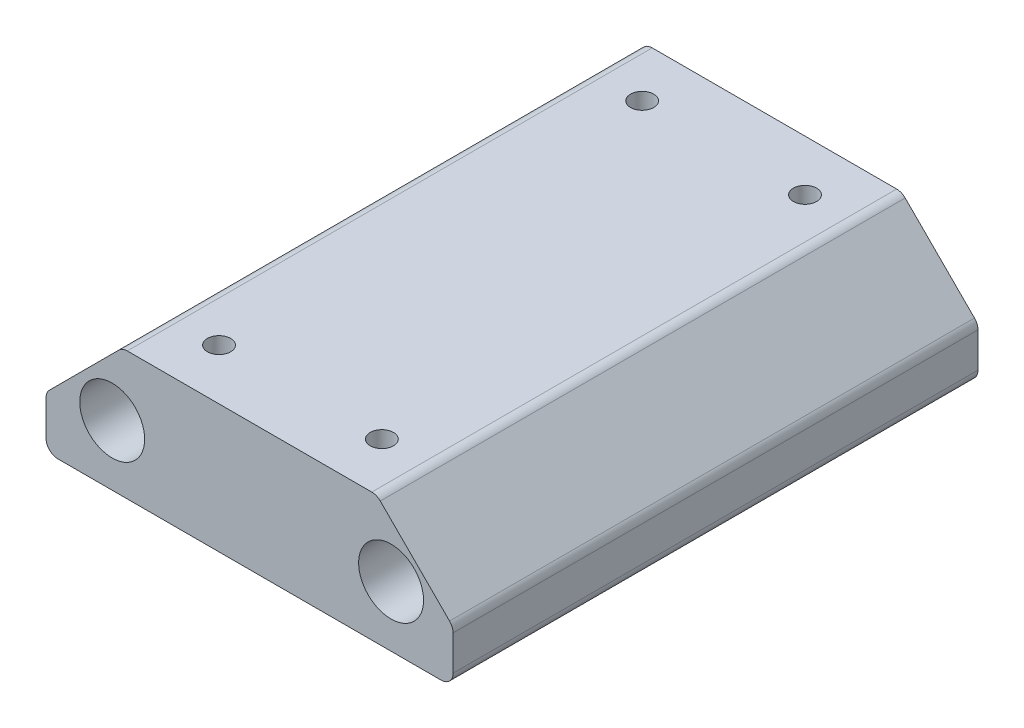
SolidWorks part; units mm, degrees
ref_plane "Front Plane" through (0, 0, 0) normal (0, 0, 1) x (1, 0, 0)
ref_plane "Top Plane" through (0, 0, 0) normal (0, 1, 0) x (1, 0, 0)
ref_plane "Right Plane" through (0, 0, 0) normal (1, 0, 0) x (0, 0, -1)
sketch "Sketch1" plane through (0, 0, 0) normal (0, 0, 1) x (1, 0, 0)
  line L1 (-25.6621, -156.15) -> (25.1379, -156.15)
  line L2 (-25.6621, -156.15) -> (-25.6621, -140.15)
  line L3 (-25.6621, -140.15) -> (25.1379, -140.15)
  line L4 (25.1379, -156.15) -> (25.1379, -140.15)
  circle A2 centre (-17.4, -148.6184) radius 4.05
  circle A3 centre (17.4, -148.6184) radius 4.05
  dimension "D1" = 16
  dimension "D2" = 50.8
extrude "Boss-Extrude1" add sketch "Sketch1" along normal up to surface (65.5 mm away)
fillet "Fillet1" radius 1.5 2 edges at (-25.6621, -156.15, 32.75) (25.1379, -156.15, 32.75)
chamfer "Chamfer1" distance 9.525 angle 45 2 edges at (25.1379, -140.15, 32.75) (-25.6621, -140.15, 32.75)
fillet "Fillet2" radius 1.5 4 edges at (25.1379, -149.675, 32.75) (15.6129, -140.15, 32.75) (-16.1371, -140.15, 32.75) (-25.6621, -149.675, 32.75)
sketch "Sketch3" plane through (0, -156.15, 0) normal (0, -1, 0) x (1, 0, 0)
  line L0 (-24.1621, 65.5) -> (23.6379, 65.5) construction
  line L1 (-10.4221, 59.15) -> (9.8979, 59.15) construction
  line L2 (-10.4221, 59.15) -> (-10.4221, 6.35) construction
  line L3 (-10.4221, 6.35) -> (9.8979, 6.35) construction
  line L4 (9.8979, 59.15) -> (9.8979, 6.35) construction
  line L5 (-24.1621, 0) -> (23.6379, 0) construction
  line L6 (25.1379, 65.5) -> (25.1379, 0) construction
  line L7 (-25.6621, 0) -> (-25.6621, 65.5) construction
  circle A0 centre (-10.4221, 59.15) radius 1.45
  circle A1 centre (9.8979, 59.15) radius 1.45
  circle A2 centre (-10.4221, 6.35) radius 1.45
  circle A3 centre (9.8979, 6.35) radius 1.45
  dimension "D1" = 2.9
  dimension "D2" = 6.35
  dimension "D3" = 6.35
  dimension "D4" = 15.24
  dimension "D5" = 15.24
extrude "Cut-Extrude1" cut sketch "Sketch3" against normal through all
ref_plane "Plane1" through (-45.4237, -144.0655, 0) normal (-0.3007, -0.9537, 0) x (0, 0, -1)
sketch "Sketch4" plane through (-45.4237, -144.0655, 0) normal (-0.3007, -0.9537, 0) x (0, 0, -1)
  line L0 (0, 20.7206) -> (-38.1, 20.7206)
  line L1 (0, 20.7206) -> (0, -26.9044)
  line L2 (-38.1, 20.7206) -> (-38.1, -26.9044)
  line L3 (0, -26.9044) -> (-38.1, -26.9044)
  line L4 (-65.5, 20.7206) -> (0, 20.7206) construction
  dimension "D1" = 38.1
  dimension "D2" = 47.625
extrude "Boss-Extrude2" [suppressed] add sketch "Sketch4" against normal blind 6
sketch "Sketch5" [suppressed] plane through (0, 0, 0) normal (0, 0, -1) x (-1, 0, 0)
  line L0 (25.2227, -149.2356) -> (16.5764, -140.5893) construction
  line L1 (23.8579, -144.574) -> (25.3908, -149.4359) construction
  line L2 (25.2227, -149.2356) -> (21.3514, -145.3643)
  line L3 (23.8579, -144.574) -> (25.3908, -149.4359)
  line L4 (23.8579, -144.574) -> (21.3514, -145.3643)
  line L5 (69.2786, -130.2529) -> (23.8579, -144.574) construction
  arc A0 (25.3908, -149.4359) -> (25.2227, -149.2356) centre (24.1621, -150.2963) ccw construction
  arc A1 (25.3908, -149.4359) -> (25.2227, -149.2356) centre (24.1621, -150.2963) ccw
extrude "Boss-Extrude3" [suppressed] add sketch "Sketch5" against normal up to surface (38.1 mm away)
fillet "Fillet3" [suppressed] radius 2.54
fillet "Fillet5" [suppressed] radius 50.8
fillet "Fillet6" [suppressed] radius 12.7
sketch "Sketch7" [suppressed] plane through (-45.4237, -144.0655, 0) normal (-0.3007, -0.9537, 0) x (0.9537, -0.3007, 0)
  line L0 (-18.9044, 0) -> (4.0956, 0)
  line L1 (-18.9044, 0) -> (-18.9044, 28)
  line L2 (4.0956, 0) -> (4.0956, 28)
  line L3 (-17.4044, 29.5) -> (2.5956, 29.5)
  line L4 (-26.9044, 0) -> (20.7206, 0) construction
  line L5 (-26.9044, 38.1) -> (-26.9044, 0) construction
  arc A0 (4.0956, 28) -> (2.5956, 29.5) centre (2.5956, 28) ccw
  arc A1 (-18.9044, 28) -> (-17.4044, 29.5) centre (-17.4044, 28) cw
  point P10 (4.0956, 29.5)
  point P13 (-18.9044, 29.5)
  dimension "D4" = 1.5
  dimension "D1" = 8
  dimension "D2" = 23
  dimension "D3" = 29.5
extrude "Cut-Extrude3" [suppressed] cut sketch "Sketch7" against normal blind 6
sketch "Sketch9" [suppressed] plane through (-45.4237, -144.0655, 0) normal (-0.3007, -0.9537, 0) x (0.9537, -0.3007, 0)
  line L0 (-3.0919, 0) -> (-3.0919, 4.625) construction
  line L1 (-26.9044, 0) -> (20.7206, 0) construction
  line L2 (-7.7169, 0) -> (-7.7169, 4.625)
  line L3 (1.5331, 0) -> (1.5331, 4.625)
  arc A0 (-7.7169, 0) -> (1.5331, 0) centre (-3.0919, 0) ccw
  arc A1 (1.5331, 4.625) -> (-7.7169, 4.625) centre (-3.0919, 4.625) ccw
  point P4 (-3.0919, 2.3125)
  dimension "D1" = 4.625
  dimension "D2" = 4.625
extrude "Cut-Extrude4" [suppressed] cut sketch "Sketch9" against normal through all
sketch "Sketch10" plane through (0, 0, 0) normal (0, 0, -1) x (-1, 0, 0)
  line L8 (25.6621, -154.65) -> (25.6621, -150.2963)
  line L16 (25.6621, -154.65) -> (25.6621, -150.2963)
  line L19 (25.2227, -149.2356) -> (16.5764, -140.5893)
  line L20 (25.2227, -149.2356) -> (16.5764, -140.5893)
  line L21 (15.5158, -140.15) -> (-14.9916, -140.15)
  line L22 (15.5158, -140.15) -> (-14.9916, -140.15)
  line L23 (-16.0523, -140.5893) -> (-24.6986, -149.2356)
  line L24 (-16.0523, -140.5893) -> (-24.6986, -149.2356)
  line L25 (-25.1379, -150.2963) -> (-25.1379, -154.65)
  line L26 (-25.1379, -150.2963) -> (-25.1379, -154.65)
  line L27 (-23.6379, -156.15) -> (24.1621, -156.15)
  line L28 (-23.6379, -156.15) -> (24.1621, -156.15)
  arc A1 (26.6378, -150.0539) -> (143.2694, 51.9579) centre (0, 0) ccw construction
  arc A2 (64.6781, -137.9946) -> (70.767, -134.9733) centre (0, 0) ccw
  arc A8 (25.6621, -150.2963) -> (25.2227, -149.2356) centre (24.1621, -150.2963) ccw
  arc A9 (25.6621, -150.2963) -> (25.2227, -149.2356) centre (24.1621, -150.2963) ccw
  arc A10 (16.5764, -140.5893) -> (15.5158, -140.15) centre (15.5158, -141.65) ccw
  arc A11 (16.5764, -140.5893) -> (15.5158, -140.15) centre (15.5158, -141.65) ccw
  arc A12 (-14.9916, -140.15) -> (-16.0523, -140.5893) centre (-14.9916, -141.65) ccw
  arc A13 (-14.9916, -140.15) -> (-16.0523, -140.5893) centre (-14.9916, -141.65) ccw
  arc A14 (-24.6986, -149.2356) -> (-25.1379, -150.2963) centre (-23.6379, -150.2963) ccw
  arc A15 (-24.6986, -149.2356) -> (-25.1379, -150.2963) centre (-23.6379, -150.2963) ccw
  arc A16 (-25.1379, -154.65) -> (-23.6379, -156.15) centre (-23.6379, -154.65) ccw
  arc A17 (-25.1379, -154.65) -> (-23.6379, -156.15) centre (-23.6379, -154.65) ccw
  arc A18 (24.1621, -156.15) -> (25.6621, -154.65) centre (24.1621, -154.65) ccw
  arc A19 (24.1621, -156.15) -> (25.6621, -154.65) centre (24.1621, -154.65) ccw
  dimension "D1" = 0
extrude "Cut-Extrude5" [suppressed] cut sketch "Sketch10" against normal through all both and the other way through all
